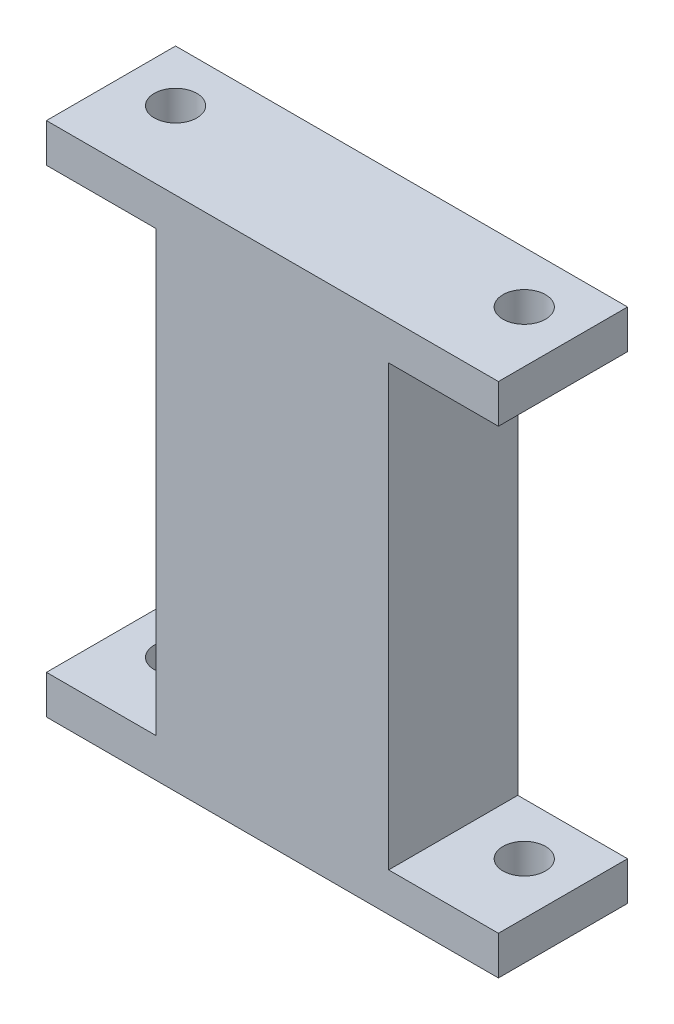
SolidWorks part; units mm, degrees
ref_plane "Front Plane" through (0, 0, 0) normal (0, 0, 1) x (1, 0, 0)
ref_plane "Top Plane" through (0, 0, 0) normal (0, 1, 0) x (1, 0, 0)
ref_plane "Right Plane" through (0, 0, 0) normal (1, 0, 0) x (0, 0, -1)
sketch "Sketch1" plane through (0, 0, 0) normal (0, 1, 0) x (1, 0, 0)
  line L1 (-17.5, -5) -> (17.5, -5)
  line L2 (-17.5, -5) -> (-17.5, 5)
  line L3 (-17.5, 5) -> (17.5, 5)
  line L4 (17.5, -5) -> (17.5, 5)
  line L5 (-17.5, -5) -> (17.5, 5) construction
  line L6 (-17.5, 5) -> (17.5, -5) construction
  point P0 (0, 0)
  dimension "D1" = 35
  dimension "D2" = 10
extrude "Boss-Extrude1" add sketch "Sketch1" along normal mid plane 3
sketch "Sketch2" plane through (0, 1.5, 0) normal (0, 1, 0) x (1, 0, 0)
  line L1 (-17.5, 5) -> (-17.5, -5) construction
  line L2 (0, 0) -> (-5.8518, 0) construction
  line L3 (0, 0) -> (0, -5.0733) construction
  circle A0 centre (-13.5, 1) radius 1.65
  circle A1 centre (13.5, 1) radius 1.65
  dimension "D1" = 3.3
  dimension "D2" = 1
  dimension "D3" = 4
extrude "Cut-Extrude1" cut sketch "Sketch2" against normal up to surface (3 mm away) up to face at (0, -1.5, 0)
sketch "Sketch3" plane through (0, 1.5, 0) normal (0, 1, 0) x (1, 0, 0)
  line L0 (-17.5, -5) -> (17.5, -5) construction
  line L1 (9, 5) -> (-9, 5)
  line L2 (9, 5) -> (9, -5)
  line L3 (9, -5) -> (-9, -5)
  line L4 (-9, 5) -> (-9, -5)
  line L5 (9, 5) -> (-9, -5) construction
  line L6 (9, -5) -> (-9, 5) construction
  point P0 (0, 0)
  dimension "D1" = 18
extrude "Boss-Extrude2" add sketch "Sketch3" along normal blind 34
ref_plane "Plane1" through (0, 18.5, 0) normal (0, 1, 0) x (1, 0, 0)
mirror "Mirror1" about plane through (0, 18.5, 0) normal (0, 1, 0) of "Cut-Extrude1", "Boss-Extrude1"
